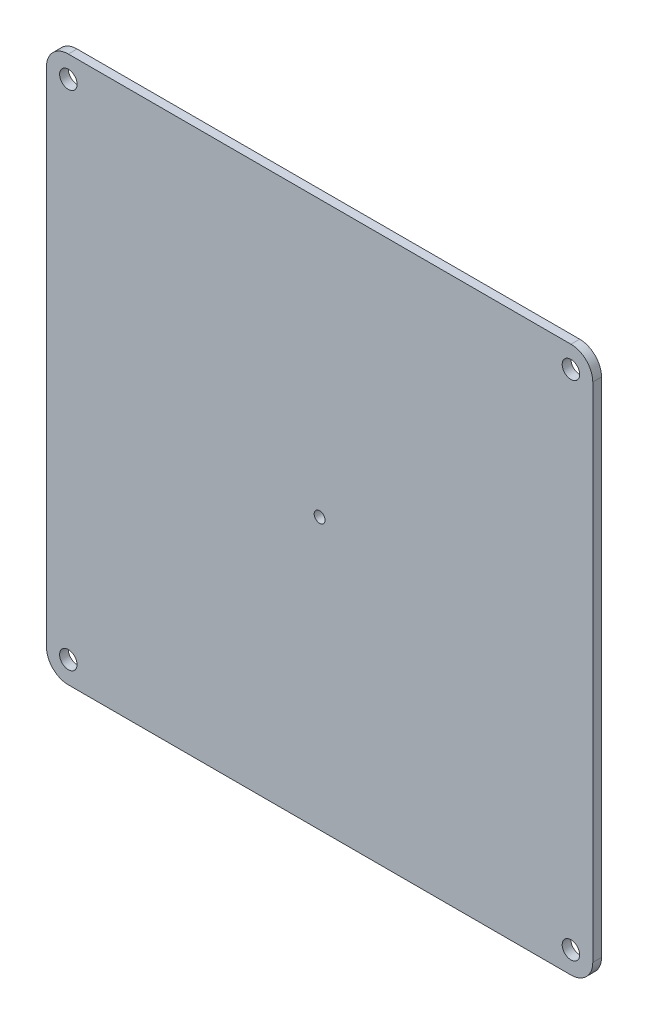
SolidWorks part; units mm, degrees
material "SEE NOTE"
ref_plane "Front Plane" through (0, 0, 0) normal (0, 0, 1) x (1, 0, 0)
ref_plane "Top Plane" through (0, 0, 0) normal (0, 1, 0) x (1, 0, 0)
ref_plane "Right Plane" through (0, 0, 0) normal (1, 0, 0) x (0, 0, -1)
sketch "Sketch1" plane through (0, 0, 0) normal (0, 0, 1) x (1, 0, 0)
  line L0 (-111.1668, 0) -> (0, 0) construction
  line L1 (46, -50) -> (-46, -50)
  line L2 (50, -46) -> (50, 46)
  line L3 (46, 50) -> (-46, 50)
  line L4 (-50, -46) -> (-50, 46)
  line L5 (50, -50) -> (-50, 50) construction
  line L6 (50, 50) -> (-50, -50) construction
  line L7 (0, 0) -> (0, 84.5875) construction
  circle A0 centre (-46, 46) radius 1.6
  circle A1 centre (0, -0.4) radius 1
  circle A2 centre (46, 46) radius 1.6
  circle A3 centre (46, -46) radius 1.6
  circle A4 centre (-46, -46) radius 1.6
  arc A5 (50, 46) -> (46, 50) centre (46, 46) ccw
  arc A6 (46, -50) -> (50, -46) centre (46, -46) ccw
  arc A7 (-46, -50) -> (-50, -46) centre (-46, -46) cw
  arc A8 (-46, 50) -> (-50, 46) centre (-46, 46) ccw
  point P0 (0, 0)
  dimension "D2" = 2
  dimension "D3" = 3.2
  dimension "D5" = 4
  dimension "D1" = 100
  dimension "D4" = 92
  dimension "D6" = 0.4
extrude "Boss-Extrude1" add sketch "Sketch1" along normal blind 1.6
